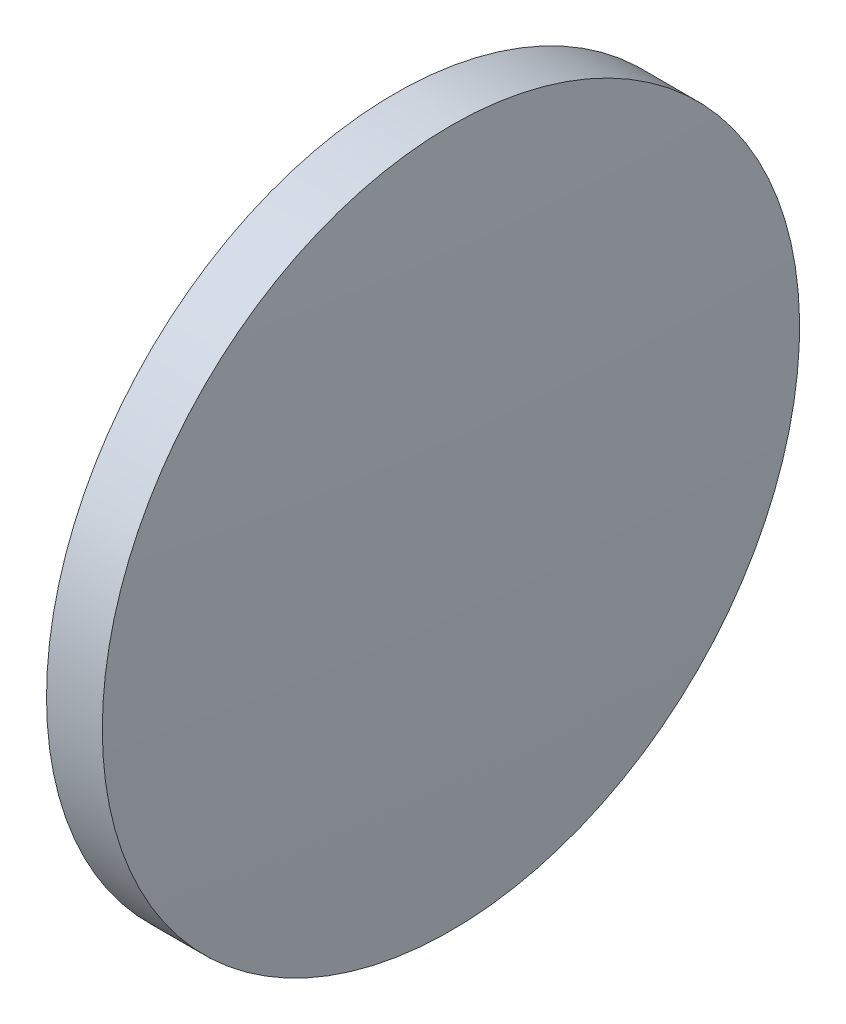
SolidWorks part; units mm, degrees
ref_plane "前视基准面" through (0, 0, 0) normal (0, 0, 1) x (1, 0, 0)
ref_plane "上视基准面" through (0, 0, 0) normal (0, 1, 0) x (1, 0, 0)
ref_plane "右视基准面" through (0, 0, 0) normal (1, 0, 0) x (0, 0, -1)
sketch "草图1" plane through (0, 0, 0) normal (0, 0, 1) x (1, 0, 0)
  line L0 (692.1648, 53.942) -> (700.1933, 53.942) construction
  line L1 (694.1939, 53.942) -> (694.1939, 66.442)
  line L2 (696.5739, 53.942) -> (694.1939, 53.942)
  line L5 (694.1939, 66.442) -> (696.1939, 66.442)
  arc A0 (696.5739, 53.942) -> (696.1939, 66.442) centre (490.7918, 53.942) ccw
revolve "旋转1" add sketch "草图1" angle 360 about L0
